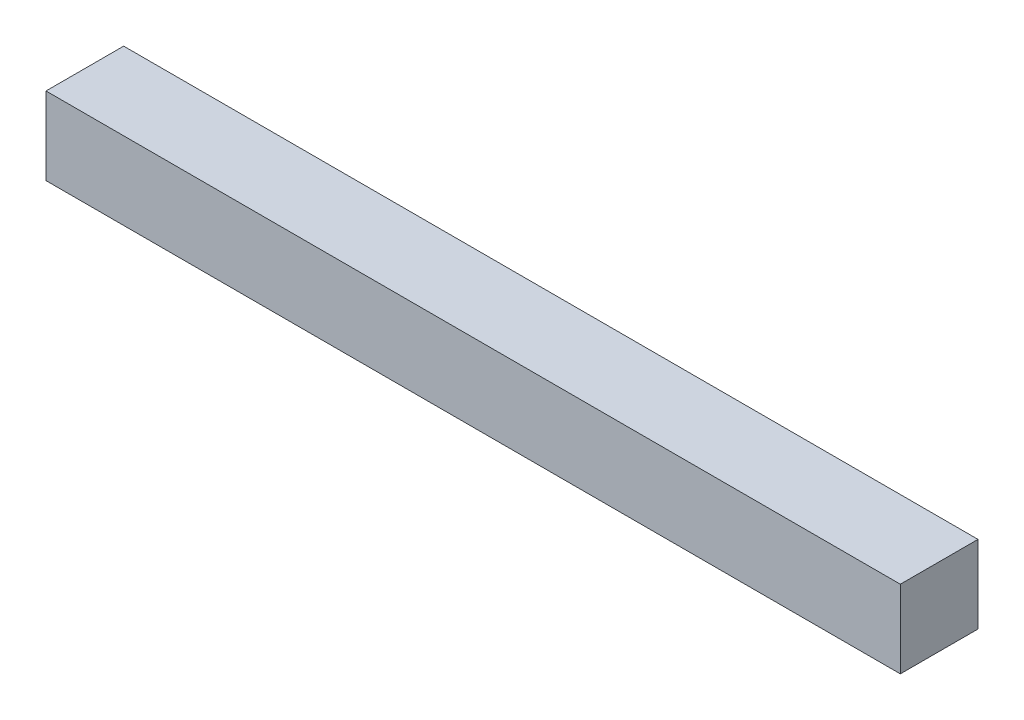
SolidWorks part; units mm, degrees
ref_plane "Front Plane" through (0, 0, 0) normal (0, 0, 1) x (1, 0, 0)
ref_plane "Top Plane" through (0, 0, 0) normal (0, 1, 0) x (1, 0, 0)
ref_plane "Right Plane" through (0, 0, 0) normal (1, 0, 0) x (0, 0, -1)
sketch "Sketch1" plane through (0, 0, 0) normal (0, 1, 0) x (1, 0, 0)
  line L1 (-139.7, -12.7) -> (139.7, -12.7)
  line L2 (-139.7, -12.7) -> (-139.7, 12.7)
  line L3 (-139.7, 12.7) -> (139.7, 12.7)
  line L4 (139.7, -12.7) -> (139.7, 12.7)
  line L5 (-139.7, -12.7) -> (139.7, 12.7) construction
  line L6 (-139.7, 12.7) -> (139.7, -12.7) construction
  point P0 (0, 0)
  dimension "D1" = 25.4
  dimension "D2" = 279.4
extrude "Boss-Extrude1" add sketch "Sketch1" along normal blind 25.4
